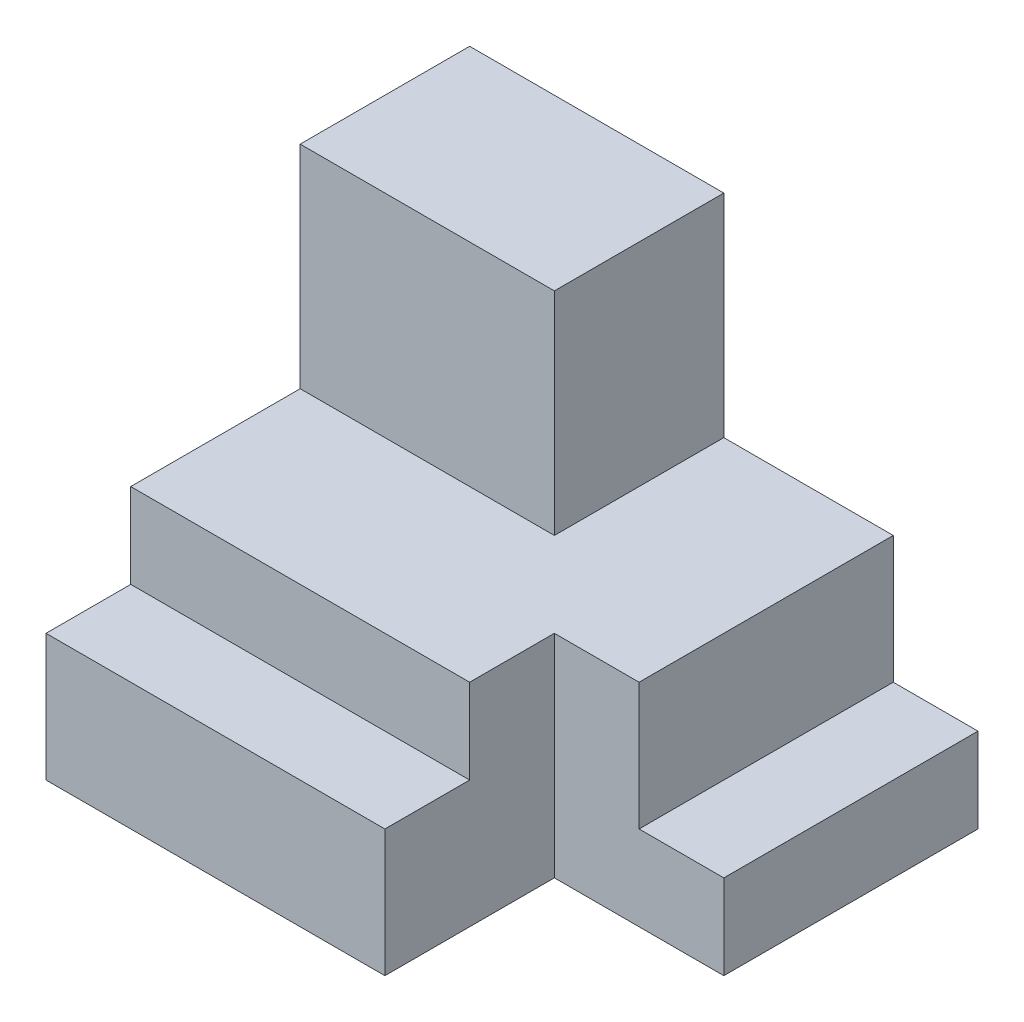
SolidWorks part; units mm, degrees
ref_plane "Front Plane" through (0, 0, 0) normal (0, 0, 1) x (1, 0, 0)
ref_plane "Top Plane" through (0, 0, 0) normal (0, 1, 0) x (1, 0, 0)
ref_plane "Right Plane" through (0, 0, 0) normal (1, 0, 0) x (0, 0, -1)
sketch "Sketch1" plane through (0, 0, 0) normal (0, 1, 0) x (1, 0, 0)
  line L0 (0, 0) -> (50.8, 0)
  line L1 (50.8, 0) -> (50.8, 25.4)
  line L2 (50.8, 25.4) -> (76.2, 25.4)
  line L3 (76.2, 25.4) -> (76.2, 63.5)
  line L4 (76.2, 63.5) -> (0, 63.5)
  line L5 (0, 63.5) -> (0, 0)
  dimension "D1" = 76.2
  dimension "D2" = 63.5
  dimension "D3" = 25.4
  dimension "D4" = 25.4
extrude "Boss-Extrude1" add sketch "Sketch1" along normal blind 31.75
sketch "Sketch3" plane through (0, 31.75, 0) normal (0, 1, 0) x (1, 0, 0)
  line L0 (76.2, 25.4) -> (76.2, 63.5) construction
  line L1 (76.2, 63.5) -> (63.5, 63.5)
  line L2 (76.2, 63.5) -> (76.2, 25.4)
  line L3 (76.2, 25.4) -> (63.5, 25.4)
  line L4 (63.5, 63.5) -> (63.5, 25.4)
  line L5 (76.2, 63.5) -> (0, 63.5) construction
  line L6 (50.8, 25.4) -> (76.2, 25.4) construction
  line L7 (50.8, 0) -> (50.8, 25.4) construction
  line L8 (0, 0) -> (50.8, 0)
  line L9 (0, 0) -> (0, 12.7)
  line L10 (0, 12.7) -> (50.8, 12.7)
  line L11 (50.8, 0) -> (50.8, 12.7)
  dimension "D1" = 12.7
  dimension "D2" = 12.7
extrude "Cut-Extrude3" cut sketch "Sketch3" along direction (0, 1, 0) on the side against the normal blind 19.05 from surface at 0 contours L2 L1 L4 L3 starting at face at (42.3333, 31.75, -29.6333)
sketch "Sketch6" plane through (0, 0, 0) normal (0, -1, 0) x (1, 0, 0)
  line L0 (50.8, 0) -> (50.8, -25.4) construction
  line L1 (0, 0) -> (50.8, 0)
  line L2 (0, 0) -> (0, -12.7)
  line L3 (0, -12.7) -> (50.8, -12.7)
  line L4 (50.8, 0) -> (50.8, -12.7)
  dimension "D1" = 12.7
extrude "Cut-Extrude5" cut sketch "Sketch6" against normal blind 44.45
sketch "Sketch7" plane through (0, 0, -12.7) normal (0, 0, 1) x (1, 0, 0)
  line L0 (50.8, 31.75) -> (50.8, 0) construction
  line L1 (0, 0) -> (50.8, 0)
  line L2 (0, 0) -> (0, 19.05)
  line L3 (0, 19.05) -> (50.8, 19.05)
  line L4 (50.8, 0) -> (50.8, 19.05)
  dimension "D1" = 19.05
extrude "Boss-Extrude2" add sketch "Sketch7" along normal blind 12.7
sketch "Sketch8" plane through (0, 31.75, 0) normal (0, 1, 0) x (1, 0, 0)
  line L0 (0, 38.1) -> (38.1, 38.1)
  line L1 (0, 63.5) -> (0, 12.7) construction
  line L2 (38.1, 38.1) -> (38.1, 63.5)
  line L3 (63.5, 63.5) -> (0, 63.5) construction
  line L4 (38.1, 63.5) -> (0, 63.5)
  line L5 (0, 63.5) -> (0, 38.1)
  dimension "D1" = 25.4
  dimension "D2" = 38.1
extrude "Boss-Extrude3" add sketch "Sketch8" along normal blind 31.75
